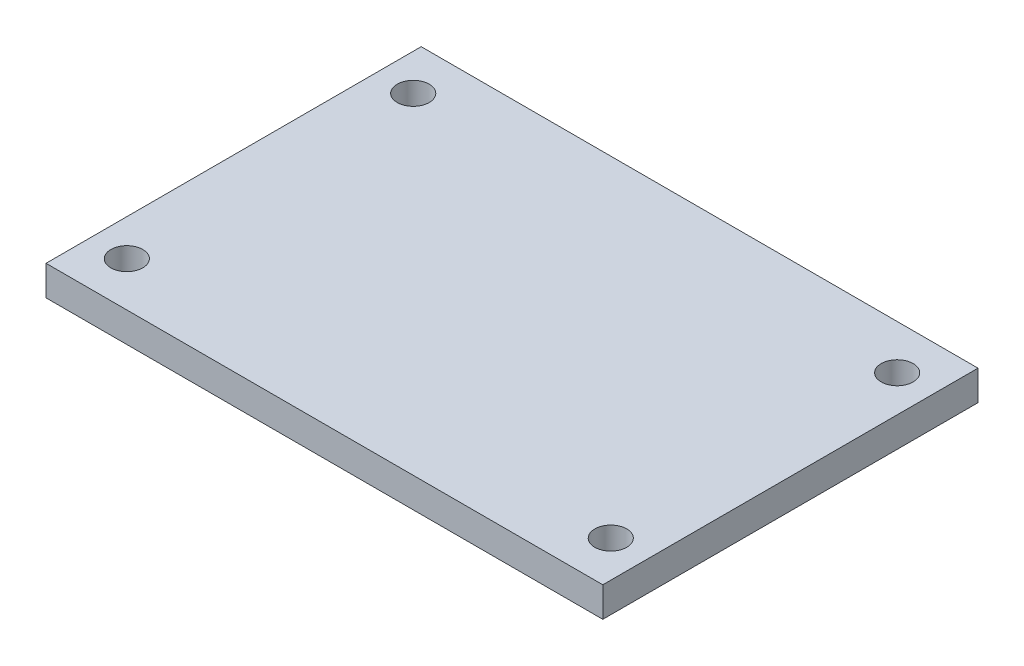
SolidWorks part; units mm, degrees
material "6061-T6 (SS)"
ref_plane "Front Plane" through (0, 0, 0) normal (0, 0, 1) x (1, 0, 0)
ref_plane "Top Plane" through (0, 0, 0) normal (0, 1, 0) x (1, 0, 0)
ref_plane "Right Plane" through (0, 0, 0) normal (1, 0, 0) x (0, 0, -1)
sketch "Sketch1" plane through (0, 0, 0) normal (0, 1, 0) x (1, 0, 0)
  line L0 (0, 37.6) -> (55.8, 37.6)
  line L1 (0, 37.6) -> (0, 0)
  line L2 (55.8, 37.6) -> (55.8, 0)
  line L3 (0, 0) -> (55.8, 0)
  line L4 (3.65, 33.15) -> (52.15, 33.15) construction
  line L5 (3.65, 33.15) -> (3.65, 4.45) construction
  line L6 (52.15, 33.15) -> (52.15, 4.45) construction
  line L7 (3.65, 4.45) -> (52.15, 4.45) construction
  point P0 (27.9, 33.15)
  point P8 (27.9, 37.6)
  point P11 (3.65, 18.8)
  point P12 (0, 18.8)
  dimension "D1" = 55.8
  dimension "D2" = 37.6
  dimension "D3" = 48.5
  dimension "D4" = 28.7
extrude "Boss-Extrude1" add sketch "Sketch1" along normal blind 3 contours L0 L2 L3 L1
sketch "Sketch4" plane through (0, 3, 0) normal (0, 1, 0) x (1, 0, 0)
  point P0 (3.65, 33.15)
  point P3 (52.15, 33.15)
  point P6 (52.15, 4.45)
  point P9 (3.65, 4.45)
hole_wizard "M3 Clearance Hole1" positions "Sketch4" profile "Sketch5" hole size "M3" standard "ANSI Metric" end condition up to next
sketch "Sketch5" plane through (3.65, 3, -33.15) normal (1, 0, 0) x (0, 0, 1)
  line L0 (0, 0) -> (0, 3)
  line L1 (0, 3) -> (1.6, 3)
  line L2 (1.6, 3) -> (1.6, 0)
  line L5 (1.6, 0) -> (0, 0)
  line L11 (0, -6.35) -> (0, 107.95) construction
  dimension "Thru Hole Dia." = 3.2
  dimension "Thru Hole Depth" = 3
